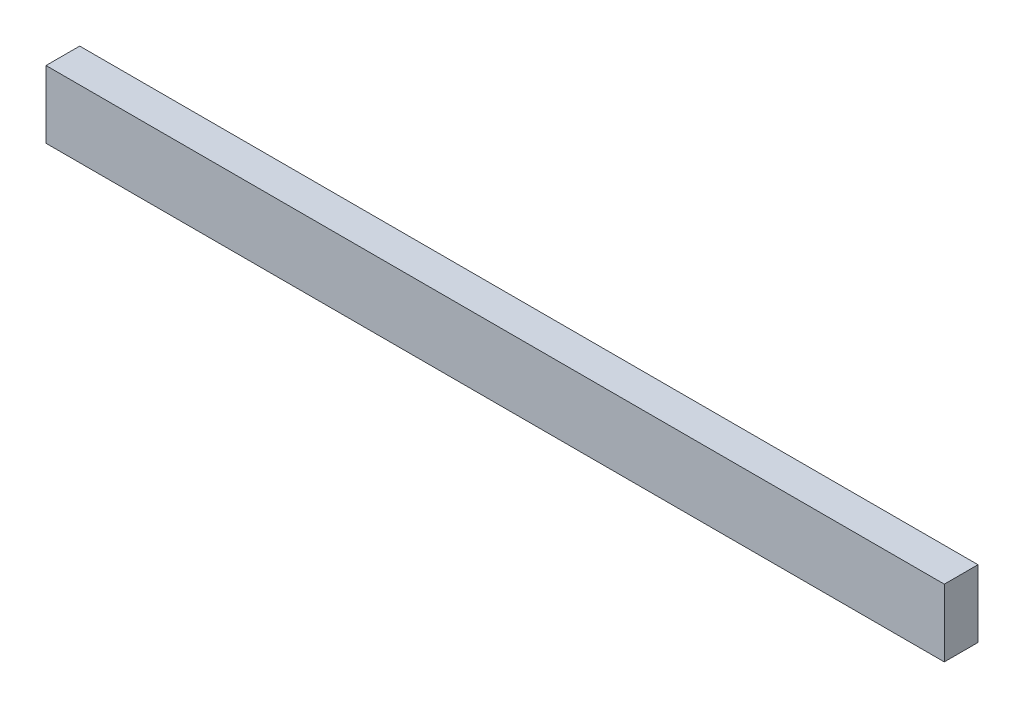
SolidWorks part; units mm, degrees
ref_plane "Front Plane" through (0, 0, 0) normal (0, 0, 1) x (1, 0, 0)
ref_plane "Top Plane" through (0, 0, 0) normal (0, 1, 0) x (1, 0, 0)
ref_plane "Right Plane" through (0, 0, 0) normal (1, 0, 0) x (0, 0, -1)
sketch "Sketch2" plane through (0, 0, 0) normal (0, 0, 1) x (1, 0, 0)
  line L1 (-40, 3) -> (40, 3)
  line L2 (-40, 3) -> (-40, -3)
  line L3 (-40, -3) -> (40, -3)
  line L4 (40, 3) -> (40, -3)
  line L5 (-40, 3) -> (40, -3) construction
  line L6 (-40, -3) -> (40, 3) construction
  point P0 (0, 0)
  dimension "D1" = 80
  dimension "D2" = 6
extrude "Boss-Extrude1" add sketch "Sketch2" along normal blind 3
